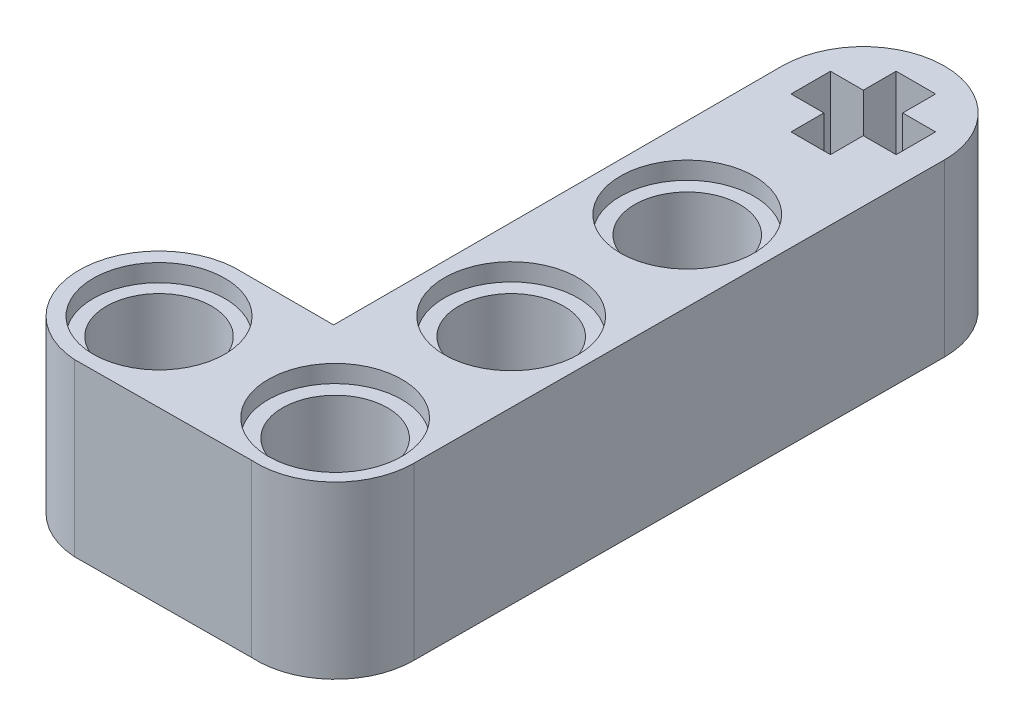
SolidWorks part; units mm, degrees
ref_plane "Front Plane" through (0, 0, 0) normal (0, 0, 1) x (1, 0, 0)
ref_plane "Top Plane" through (0, 0, 0) normal (0, 1, 0) x (1, 0, 0)
ref_plane "Right Plane" through (0, 0, 0) normal (1, 0, 0) x (0, 0, -1)
sketch "Sketch1" plane through (0, 0, 0) normal (0, 1, 0) x (1, 0, 0)
  line L0 (-3.9491, 0) -> (4.0909, 0) construction
  line L1 (-13.2691, 0) -> (13.2691, 0) construction
  line L2 (-3.7232, 3.643) -> (0.3809, 3.643)
  line L3 (-4.1749, -3.643) -> (3.8668, -3.583)
  line L4 (4.0909, 0) -> (4.0909, 24.12) construction
  line L5 (0.3809, 3.643) -> (0.3809, 24.12)
  line L6 (7.6809, 0.0072) -> (7.8009, 24.12)
  line L7 (0.3809, 8.04) -> (14.3139, 8.04) construction
  line L8 (0.3809, 16.08) -> (16.5266, 16.08) construction
  line L11 (3.1909, 26.52) -> (4.9909, 26.52)
  line L12 (3.1909, 26.52) -> (3.1909, 25.02)
  line L13 (3.1909, 21.72) -> (4.9909, 21.72)
  line L14 (4.9909, 26.52) -> (4.9909, 25.02)
  line L15 (3.1909, 26.52) -> (4.9909, 21.72) construction
  line L16 (3.1909, 21.72) -> (4.9909, 26.52) construction
  line L17 (1.6909, 25.02) -> (3.1909, 25.02)
  line L18 (1.6909, 25.02) -> (1.6909, 23.22)
  line L19 (1.6909, 23.22) -> (3.1909, 23.22)
  line L20 (6.4909, 25.02) -> (6.4909, 23.22)
  line L21 (1.6909, 25.02) -> (6.4909, 23.22) construction
  line L22 (1.6909, 23.22) -> (6.4909, 25.02) construction
  line L23 (4.9909, 25.02) -> (6.4909, 25.02)
  line L24 (4.9909, 23.22) -> (4.9909, 21.72)
  line L25 (4.9909, 23.22) -> (6.4909, 23.22)
  line L26 (3.1909, 23.22) -> (3.1909, 21.72)
  arc A0 (-3.7232, 3.643) -> (-4.1749, -3.643) centre (-3.9491, 0) ccw
  arc A1 (3.8668, -3.583) -> (7.6809, 0.0072) centre (4.0909, 0) ccw
  arc A3 (7.8009, 24.12) -> (0.3809, 24.12) centre (4.0909, 24.12) ccw
  circle A4 centre (-3.9491, 0) radius 2.4
  circle A5 centre (4.0909, 0) radius 2.4
  circle A6 centre (4.0909, 8.04) radius 2.4
  circle A7 centre (4.0909, 16.08) radius 2.4
  point P5 (0.0322, 0)
  point P12 (4.0222, 11.96)
  dimension "D3" = 8.04
  dimension "D1" = 7.3
  dimension "D2" = 15.28
extrude "Boss-Extrude2" add sketch "Sketch1" along normal blind 7.8
sketch "Sketch2" plane through (0, 7.8, 0) normal (0, 1, 0) x (1, 0, 0)
  line L0 (-4.29, 0) -> (4.29, 0) construction
  circle A0 centre (-3.9491, 0) radius 3.005
  circle A1 centre (-3.9491, 0) radius 2.4 construction
  circle A2 centre (4.0909, 0) radius 3.05
  circle A3 centre (4.0909, 0) radius 2.4 construction
  circle A5 centre (4.0909, 8.04) radius 3.05
  circle A6 centre (4.0909, 8.04) radius 2.4 construction
  circle A7 centre (4.0909, 16.08) radius 3.05
  circle A8 centre (4.0909, 16.08) radius 2.4 construction
  dimension "D1" = 0
  dimension "D2" = 0
  dimension "D3" = 0
  dimension "D4" = 0
extrude "Cut-Extrude1" cut sketch "Sketch2" against normal blind 0.8
sketch "Sketch3" plane through (0, 0, 0) normal (0, -1, 0) x (1, 0, 0)
  line L0 (4.29, 0) -> (-4.29, 0) construction
  circle A0 centre (-3.9491, 0) radius 3.05
  circle A1 centre (-3.9491, 0) radius 2.4 construction
  circle A2 centre (4.0909, 0) radius 3.05
  circle A3 centre (4.0909, 0) radius 2.4 construction
  circle A4 centre (4.0909, -8.04) radius 3.05
  circle A5 centre (4.0909, -16.08) radius 3.05
  circle A6 centre (4.0909, -16.08) radius 2.4 construction
  circle A7 centre (4.0909, -8.04) radius 2.4 construction
  dimension "D1" = 0
  dimension "D2" = 0
  dimension "D3" = 0
  dimension "D4" = 0.65
extrude "Cut-Extrude2" cut sketch "Sketch3" against normal blind 0.8
